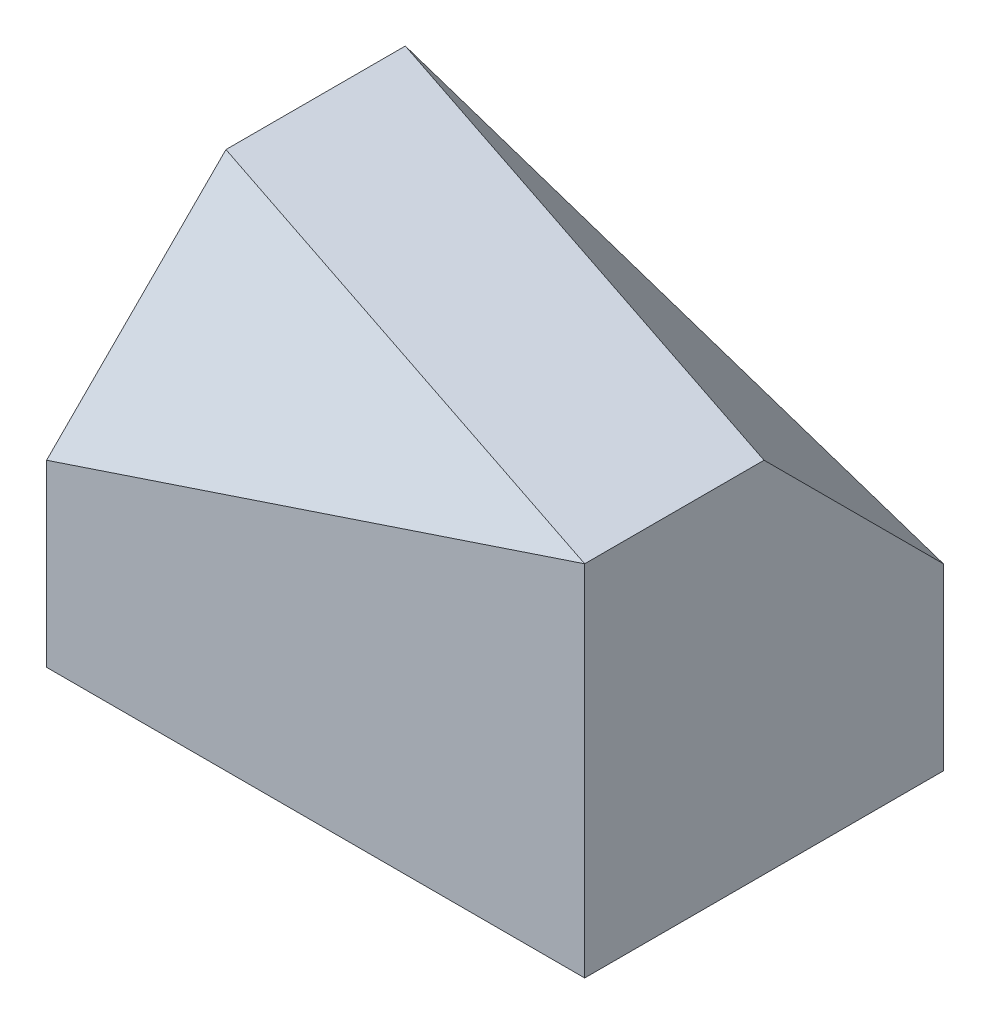
SolidWorks part; units mm, degrees
ref_plane "前基準面" through (0, 0, 0) normal (0, 0, 1) x (1, 0, 0)
ref_plane "上基準面" through (0, 0, 0) normal (0, 1, 0) x (1, 0, 0)
ref_plane "右基準面" through (0, 0, 0) normal (1, 0, 0) x (0, 0, -1)
sketch "草圖1" plane through (0, 0, 0) normal (0, 1, 0) x (1, 0, 0)
  line L1 (-3, -2) -> (3, -2)
  line L2 (-3, -2) -> (-3, 2)
  line L3 (-3, 2) -> (3, 2)
  line L4 (3, -2) -> (3, 2)
  line L5 (-3, -2) -> (3, 2) construction
  line L6 (-3, 2) -> (3, -2) construction
  point P0 (0, 0)
  dimension "D1" = 6
  dimension "D2" = 4
extrude "填料-伸長1" add sketch "草圖1" along normal blind 4
sketch "草圖2" plane through (3, 0, 0) normal (1, 0, 0) x (0, 0, -1)
  line L0 (2, 2) -> (0, 4)
  line L1 (2, 4) -> (2, 0) construction
  line L2 (-2, 4) -> (2, 4) construction
  dimension "D1" = 2
  dimension "D2" = 2
sketch "草圖4" plane through (0, 4, 0) normal (0, 1, 0) x (1, 0, 0)
  line L0 (-3, 2) -> (3, 0)
  line L1 (3, 2) -> (3, 0) construction
  dimension "D1" = 2
sketch "草圖5" plane through (0, 0, -2) normal (0, 0, -1) x (-1, 0, 0)
  line L0 (-3, 2) -> (15, 4)
  line L1 (-3, 4) -> (-3, 0) construction
  line L2 (3, 4) -> (-3, 4) construction
ref_plane "平面1" through (0.7895, 2.3684, -2.3684) normal (-0.2294, -0.6882, 0.6882) x (0.9733, -0.1622, 0.1622)
sketch "草圖6" plane through (0.7895, 2.3684, -2.3684) normal (-0.2294, -0.6882, 0.6882) x (0.9733, -0.1622, 0.1622)
  line L0 (0, 0) -> (-20.5388, 0)
  line L1 (-20.5388, 0) -> (-20.5388, 12.5352)
  line L2 (-20.5388, 12.5352) -> (11.7135, 14.6256)
  line L3 (11.7135, 14.6256) -> (12.2681, -0.2633)
  line L4 (12.2681, -0.2633) -> (0, 0)
extrude "除料-伸長1" cut sketch "草圖6" against normal blind 4
sketch "草圖8" plane through (-3, 0, 0) normal (-1, 0, 0) x (0, 0, 1)
  line L0 (2, 2) -> (0, 4)
  line L1 (2, 4) -> (2, 0) construction
  line L2 (-2, 4) -> (2, 4) construction
  dimension "D1" = 2
  dimension "D2" = 2
sketch "草圖9" plane through (0, 4, 0) normal (0, 1, 0) x (1, 0, 0)
  line L0 (-3, 0) -> (3, -2)
  line L1 (-3, 2) -> (-3, -2) construction
ref_plane "平面2" through (-0.7895, 2.3684, 2.3684) normal (-0.2294, 0.6882, 0.6882) x (0.9733, 0.1622, 0.1622)
sketch "草圖10" plane through (-0.7895, 2.3684, 2.3684) normal (-0.2294, 0.6882, 0.6882) x (0.9733, 0.1622, 0.1622)
  line L1 (-12.1828, -0.4751) -> (20.0695, -0.4751)
  line L2 (-12.1828, -0.4751) -> (-12.1828, 14.7041)
  line L3 (-12.1828, 14.7041) -> (20.0695, 14.7041)
  line L4 (20.0695, -0.4751) -> (20.0695, 14.7041)
extrude "除料-伸長2" cut sketch "草圖10" along normal blind 5
